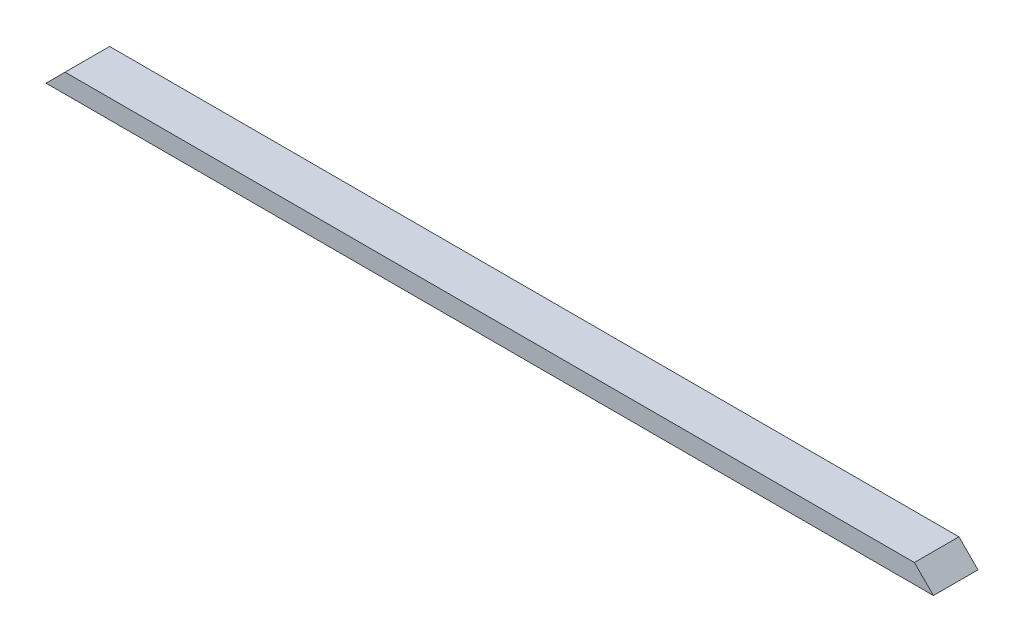
SolidWorks part; units mm, degrees
material "Pine"
ref_plane "Front Plane" through (0, 0, 0) normal (0, 0, 1) x (1, 0, 0)
ref_plane "Top Plane" through (0, 0, 0) normal (0, 1, 0) x (1, 0, 0)
ref_plane "Right Plane" through (0, 0, 0) normal (1, 0, 0) x (0, 0, -1)
sketch "Sketch1" plane through (0, 0, 0) normal (0, 1, 0) x (1, 0, 0)
  line L1 (0, 0) -> (1771.65, 0)
  line L2 (0, 0) -> (0, 88.9)
  line L3 (0, 88.9) -> (1771.65, 88.9)
  line L4 (1771.65, 0) -> (1771.65, 88.9)
  dimension "D1" = 88.9
  dimension "D2" = 1771.65
extrude "Boss-Extrude1" add sketch "Sketch1" along normal blind 38.1
sketch "Sketch2" plane through (0, 0, 0) normal (0, 0, 1) x (1, 0, 0)
  line L0 (0, 0) -> (38.1, 38.1)
  line L1 (0, 38.1) -> (1771.65, 38.1) construction
  line L2 (38.1, 38.1) -> (0, 38.1)
  line L3 (0, 38.1) -> (0, 0)
  line L5 (1771.65, 0) -> (1771.65, 38.1)
  line L9 (1771.65, 38.1) -> (1733.55, 38.1)
  line L10 (1733.55, 38.1) -> (1771.65, 0)
  dimension "D1" = 38.1
  dimension "D2" = 38.1
  dimension "D3" = 38.1
extrude "Cut-Extrude1" cut sketch "Sketch2" against normal through all
